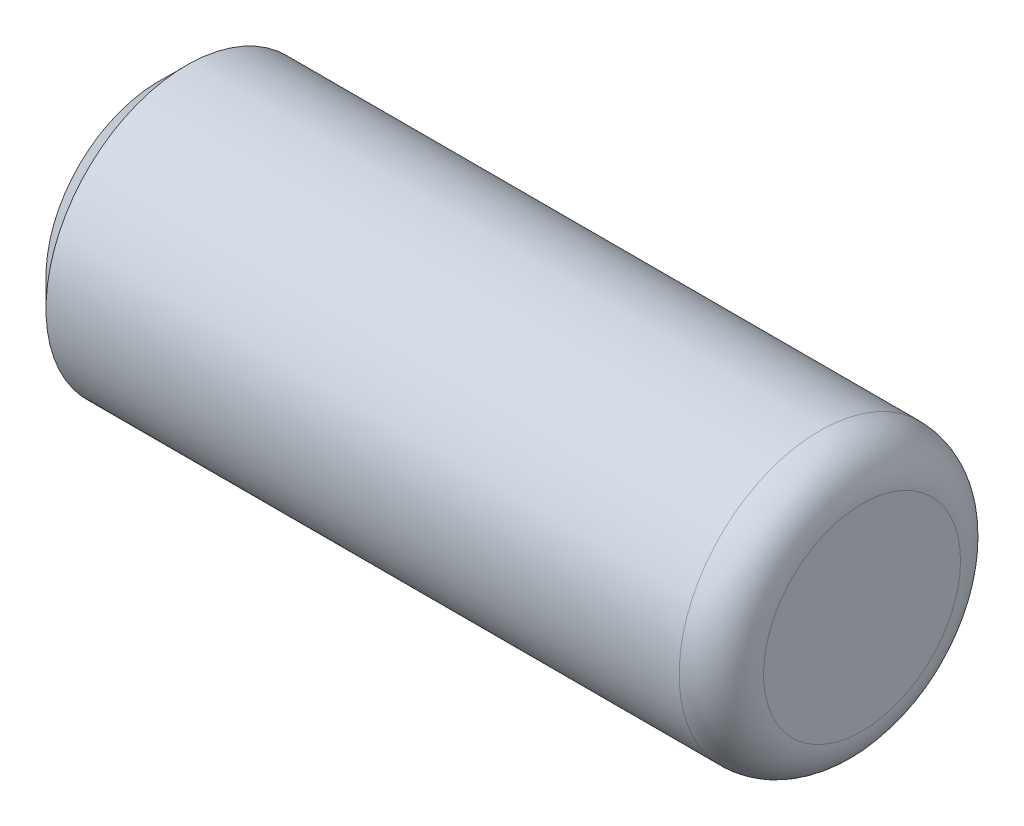
SolidWorks part; units mm, degrees
material "SUJ"
ref_plane "Front Plane" through (0, 0, 0) normal (0, 0, 1) x (1, 0, 0)
ref_plane "Top Plane" through (0, 0, 0) normal (0, 1, 0) x (1, 0, 0)
ref_plane "Right Plane" through (0, 0, 0) normal (1, 0, 0) x (0, 0, -1)
sketch "Sketch1" plane through (0, 0, 0) normal (1, 0, 0) x (0, -1, 0)
  circle A0 centre (0, 0) radius 1
  dimension "D1" = 2
extrude "Boss-Extrude1" add sketch "Sketch1" along normal mid plane 5
fillet "Fillet1" radius 0.3 1 edges at (2.5, 0, -1)
chamfer "Chamfer1" distance 0.2 angle 45 1 edges at (-2.5, 0, -1)
